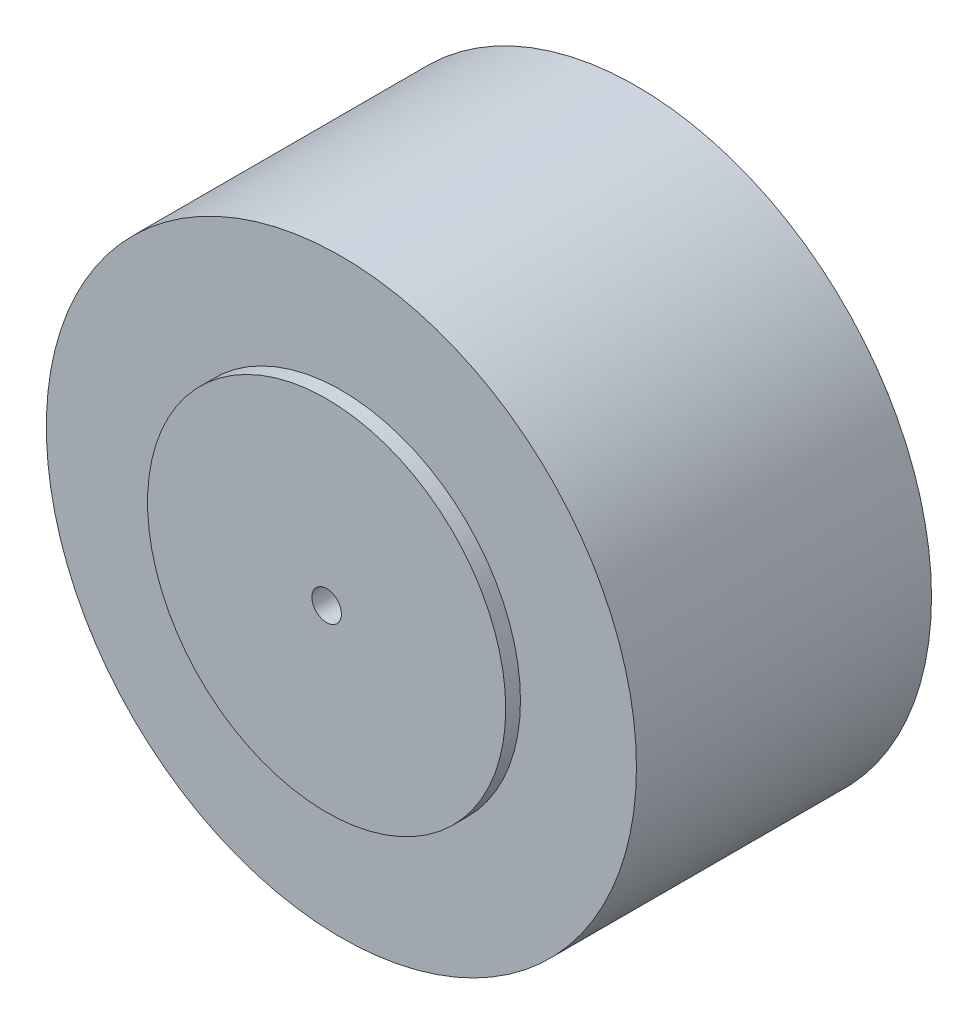
SolidWorks part; units mm, degrees
ref_plane "Front Plane" through (0, 0, 0) normal (0, 0, 1) x (1, 0, 0)
ref_plane "Top Plane" through (0, 0, 0) normal (0, 1, 0) x (1, 0, 0)
ref_plane "Right Plane" through (0, 0, 0) normal (1, 0, 0) x (0, 0, -1)
sketch "Sketch1" plane through (0, 0, 0) normal (0, 0, 1) x (1, 0, 0)
  circle A0 centre (0, 0) radius 12.7
  dimension "D1" = 25.4
extrude "Boss-Extrude1" add sketch "Sketch1" along normal blind 12.7
sketch "Sketch2" plane through (0, 0, 12.7) normal (0, 0, 1) x (1, 0, 0)
  circle A0 centre (0, 0) radius 7.7083
extrude "Boss-Extrude2" add sketch "Sketch2" along normal blind 0.635
sketch "Sketch3" plane through (0, 0, 0) normal (0, 0, -1) x (-1, 0, 0)
  circle A0 centre (0, 0) radius 7.678
extrude "Boss-Extrude3" add sketch "Sketch3" along normal blind 0.635
sketch "Sketch4" plane through (0, 0, 13.335) normal (0, 0, 1) x (1, 0, 0)
  circle A1 centre (0, 0) radius 0.635
  dimension "D1" = 1.27
extrude "Cut-Extrude1" cut sketch "Sketch4" against normal blind 1.27
sketch "Sketch5" plane through (0, 0, -0.635) normal (0, 0, -1) x (-1, 0, 0)
  circle A0 centre (0, 0) radius 0.635
  dimension "D1" = 1.27
extrude "Cut-Extrude2" cut sketch "Sketch5" against normal blind 1.27
